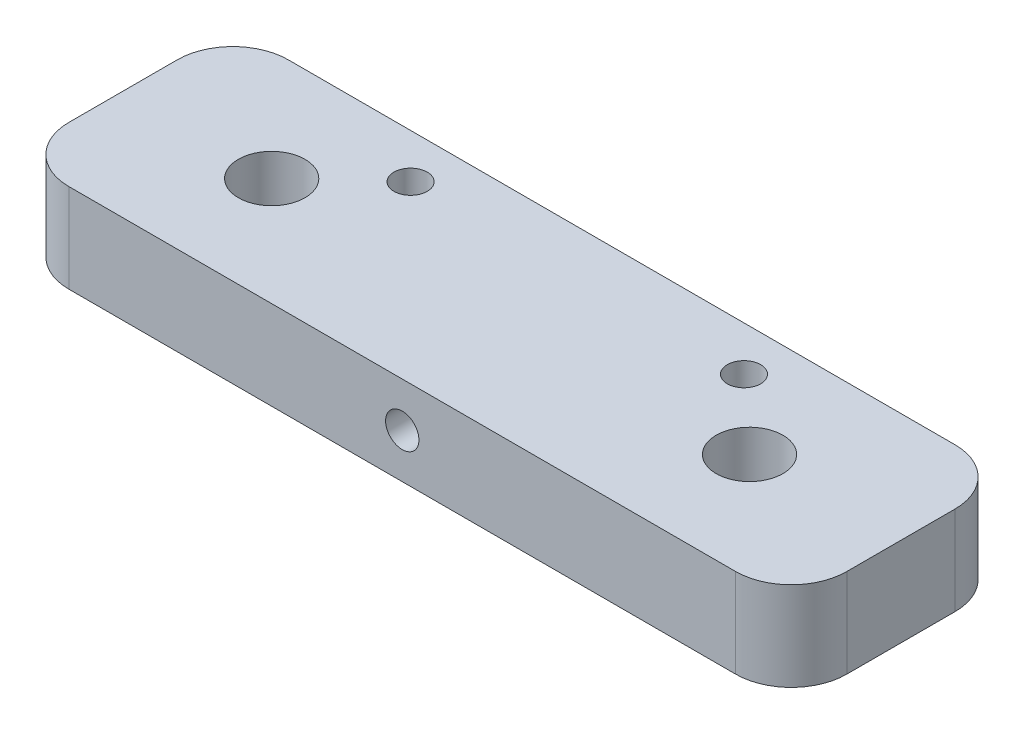
SolidWorks part; units mm, degrees
ref_plane "前视基准面" through (0, 0, 0) normal (0, 0, 1) x (1, 0, 0)
ref_plane "上视基准面" through (0, 0, 0) normal (0, 1, 0) x (1, 0, 0)
ref_plane "右视基准面" through (0, 0, 0) normal (1, 0, 0) x (0, 0, -1)
sketch "草图1" plane through (0, 0, 0) normal (0, 1, 0) x (1, 0, 0)
  line L1 (-35, -9.875) -> (35, -9.875)
  line L2 (-35, -9.875) -> (-35, 9.875)
  line L3 (-35, 9.875) -> (35, 9.875)
  line L4 (35, -9.875) -> (35, 9.875)
  line L5 (-35, -9.875) -> (35, 9.875) construction
  line L6 (-35, 9.875) -> (35, -9.875) construction
  point P0 (0, 0)
  dimension "D1" = 70
  dimension "D2" = 19.75
extrude "凸台-拉伸1" add sketch "草图1" along normal blind 8
sketch "草图2" plane through (0, 8, 0) normal (0, 1, 0) x (1, 0, 0)
  line L0 (0, 27.7349) -> (0, -22.8781) construction
  line L1 (-24.5, -0.125) -> (-24.5, -9.875) construction
  line L2 (-35, -9.875) -> (35, -9.875) construction
  line L3 (-24.5, -9.875) -> (-23.5, -9.875) construction
  line L4 (-23.5, -9.875) -> (-23.5, -2.3611) construction
  line L5 (23.5, -9.875) -> (23.5, -2.3611) construction
  line L6 (24.5, -9.875) -> (23.5, -9.875) construction
  line L7 (24.5, -0.125) -> (24.5, -9.875) construction
  line L8 (35, 9.875) -> (-35, 9.875) construction
  arc A0 (-23.5, -2.3611) -> (-24.5, -0.125) centre (-21.5, -0.125) ccw construction
  arc A1 (23.5, -2.3611) -> (24.5, -0.125) centre (21.5, -0.125) cw construction
  arc A2 (-24.5, -0.125) -> (-23.5, -2.3611) centre (-21.5, -0.125) ccw construction
  arc A3 (23.5, -2.3611) -> (24.5, -0.125) centre (21.5, -0.125) cw construction
  arc A4 (24.5, -0.125) -> (23.5, -2.3611) centre (21.5, -0.125) cw construction
  circle A6 centre (-21.5, -0.125) radius 3
  circle A7 centre (21.5, -0.125) radius 3
  dimension "D1" = 43
  dimension "D2" = 6
  dimension "D3" = 1
  dimension "D4" = 10
extrude "切除-拉伸1" cut sketch "草图2" against normal through all
sketch "草图9" plane through (0, 8, 0) normal (0, 1, 0) x (1, 0, 0)
  line L0 (0, 16.9657) -> (0, -15.7004) construction
  line L1 (35, 9.875) -> (-35, 9.875) construction
  line L2 (-35, 9.875) -> (-35, -9.875) construction
  circle A0 centre (-15, 5.875) radius 1.5
  circle A1 centre (15, 5.875) radius 1.5
  dimension "D3" = 3
  dimension "D1" = 4
  dimension "D2" = 20
extrude "切除-拉伸7" cut sketch "草图9" against normal through all
sketch "草图10" plane through (0, 0, -9.875) normal (0, 0, -1) x (-1, 0, 0)
  line L0 (-35, 8) -> (35, 8) construction
  circle A0 centre (0, 4) radius 1.5
  dimension "D1" = 3
  dimension "D2" = 4
extrude "切除-拉伸8" cut sketch "草图10" against normal through all
fillet "圆角1" radius 5 4 edges at (35, 4, 9.875) (-35, 4, 9.875) (-35, 4, -9.875) (35, 4, -9.875)
sketch "草图11" plane through (0, 0, -9.875) normal (0, 0, -1) x (-1, 0, 0)
  circle A0 centre (0, 4) radius 3.5
  dimension "D1" = 7
extrude "切除-拉伸9" cut sketch "草图11" against normal blind 2
equation "\"2、\"=10"
